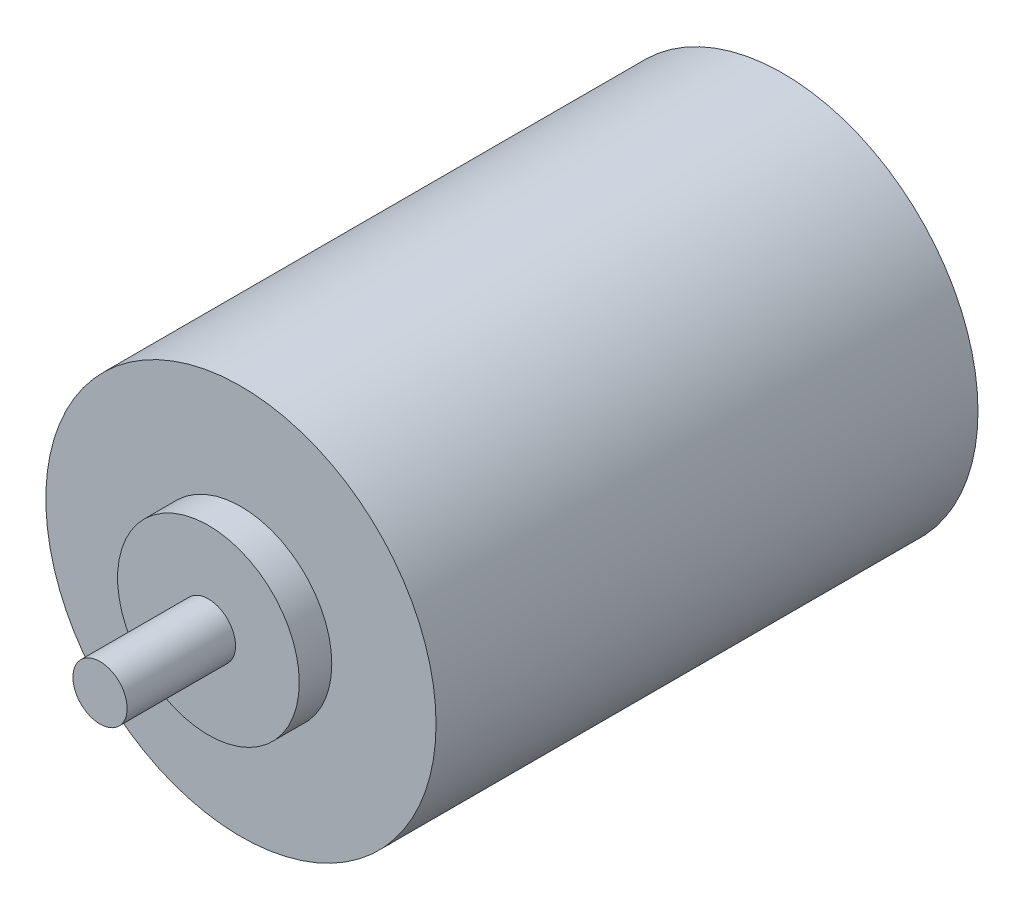
SolidWorks part; units mm, degrees
ref_plane "Front Plane" through (0, 0, 0) normal (0, 0, 1) x (1, 0, 0)
ref_plane "Top Plane" through (0, 0, 0) normal (0, 1, 0) x (1, 0, 0)
ref_plane "Right Plane" through (0, 0, 0) normal (1, 0, 0) x (0, 0, -1)
sketch "Sketch1" plane through (0, 0, 0) normal (0, 0, 1) x (1, 0, 0)
  circle A0 centre (0, 0) radius 18
  dimension "D1" = 36
extrude "Boss-Extrude1" add sketch "Sketch1" along normal blind 50
sketch "Sketch2" plane through (0, 0, 50) normal (0, 0, 1) x (1, 0, 0)
  circle A0 centre (0, 0) radius 8.3808
extrude "Boss-Extrude2" add sketch "Sketch2" along normal blind 3
sketch "Sketch3" plane through (0, 0, 53) normal (0, 0, 1) x (1, 0, 0)
  circle A0 centre (0, 0) radius 2.5
  dimension "D1" = 5
extrude "Boss-Extrude3" add sketch "Sketch3" along normal blind 10
